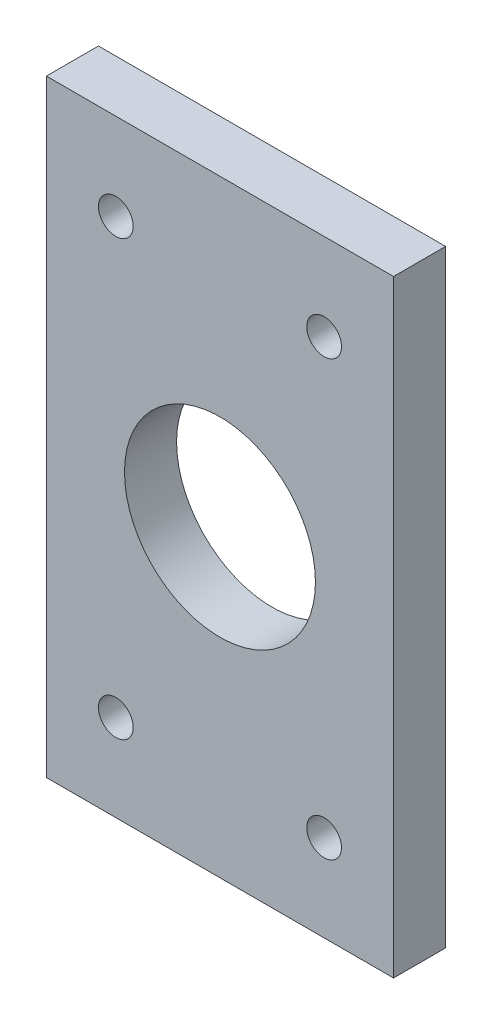
SolidWorks part; units mm, degrees
ref_plane "Front" through (0, 0, 0) normal (0, 0, 1) x (1, 0, 0)
ref_plane "Top" through (0, 0, 0) normal (0, 1, 0) x (1, 0, 0)
ref_plane "Right" through (0, 0, 0) normal (1, 0, 0) x (0, 0, -1)
sketch "草图1" plane through (0, 0, 0) normal (0, 0, 1) x (1, 0, 0)
  line L0 (-40, 0) -> (-40, 77) construction
  line L1 (-40, 44.5032) -> (-40, 114.5032)
  line L2 (0, 0) -> (0, 77) construction
  line L3 (0, 44.5032) -> (0, 114.5032)
  line L4 (-40, 114.5032) -> (0, 114.5032)
  line L6 (-40, 44.5032) -> (0, 44.5032)
  circle A1 centre (-20, 79.5032) radius 11
  point P8 (-40, 79.5032)
  point P10 (0, 0)
  point P11 (-20, 79.5032)
  point P13 (-20, 35)
  dimension "D1" = 70
extrude "凸台-拉伸1" add sketch "草图1" along normal blind 6 contours A1 | L1 L4 L3 L6
sketch "草图2" plane through (0, 0, 6) normal (0, 0, 1) x (1, 0, 0)
  line L0 (-32, 104.5032) -> (-8, 104.5032) construction
  line L1 (-40, 114.5032) -> (0, 114.5032) construction
  circle A0 centre (-32, 104.5032) radius 2
  circle A1 centre (-8, 104.5032) radius 2
  point P4 (-20, 104.5032)
  dimension "D1" = 4
  dimension "D2" = 24
  dimension "D3" = 10
extrude "切除-拉伸1" cut sketch "草图2" against normal blind 10
ref_plane "基准面1" through (0, 79.5032, 0) normal (0, 1, 0) x (1, 0, 0)
mirror "镜向1" about plane through (0, 79.5032, 0) normal (0, 1, 0) of "切除-拉伸1"
